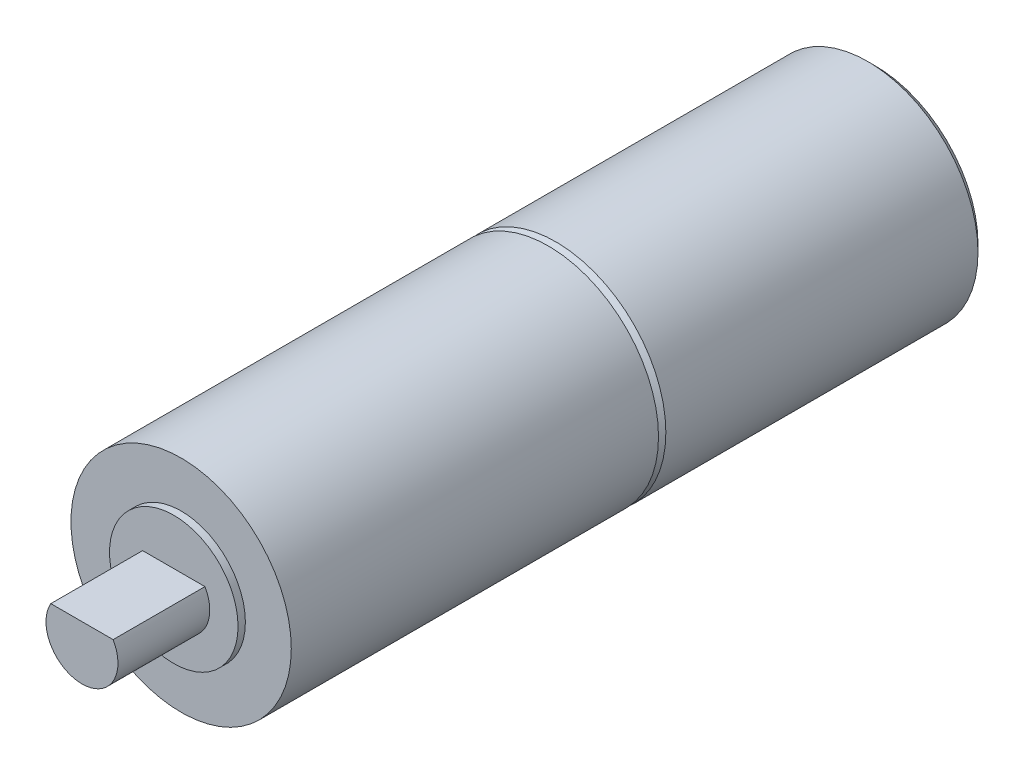
SolidWorks part; units mm, degrees
ref_plane "Front Plane" through (0, 0, 0) normal (0, 0, 1) x (1, 0, 0)
ref_plane "Top Plane" through (0, 0, 0) normal (0, 1, 0) x (1, 0, 0)
ref_plane "Right Plane" through (0, 0, 0) normal (1, 0, 0) x (0, 0, -1)
sketch "Sketch1" plane through (0, 0, 0) normal (0, 0, 1) x (1, 0, 0)
  circle A0 centre (0, 0) radius 3
extrude "Boss-Extrude1" add sketch "Sketch1" along normal blind 8.9
chamfer "Chamfer1" distance 0.2 distance2 0.2 2 edges at (3, 0, 0) (3, 0, 8.9)
sketch "Sketch2" plane through (0, 0, 8.9) normal (0, 0, 1) x (1, 0, 0)
  circle A0 centre (0, 0) radius 3
extrude "Boss-Extrude2" add sketch "Sketch2" along normal blind 10
sketch "Sketch3" plane through (0, 0, 18.9) normal (0, 0, 1) x (1, 0, 0)
  circle A0 centre (0, 0) radius 1.75
extrude "Boss-Extrude3" add sketch "Sketch3" along normal blind 0.2
sketch "Sketch4" plane through (0, 0, 19.1) normal (0, 0, 1) x (1, 0, 0)
  circle A0 centre (0, 0) radius 1.5
sketch "Sketch5" plane through (0, 0, 19.1) normal (0, 0, 1) x (1, 0, 0)
  line L1 (0, 0.49) -> (0.8487, 0.49)
  line L2 (0, 0.49) -> (-0.8487, 0.49)
  arc A0 (-0.8487, 0.49) -> (0.8487, 0.49) centre (0, 0) ccw
extrude "Boss-Extrude4" add sketch "Sketch5" along normal blind 2.5
